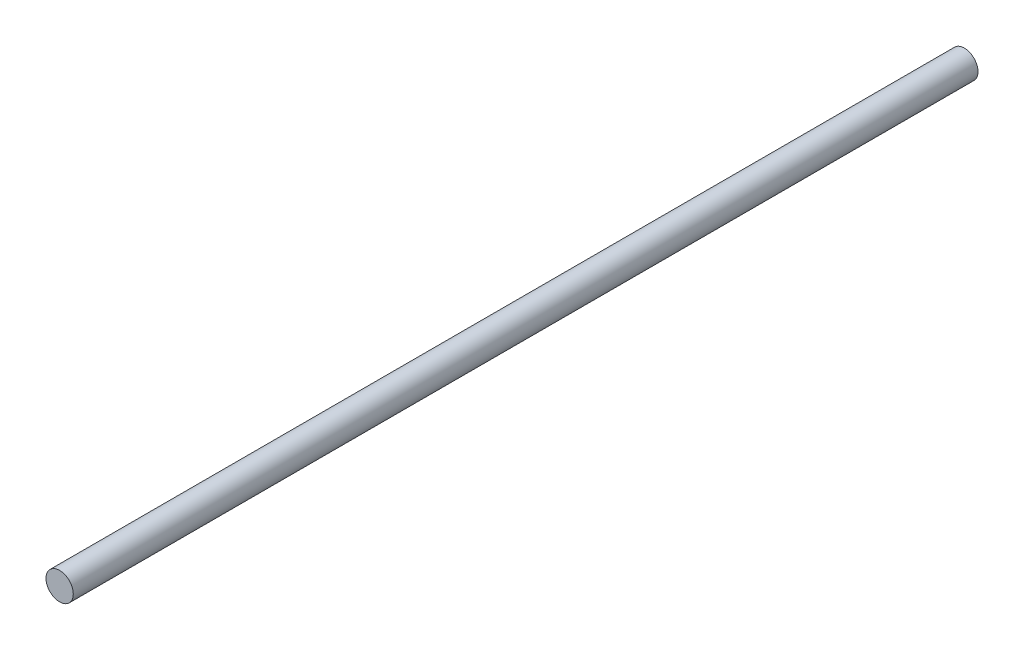
SolidWorks part; units mm, degrees
material "Alloy Steel"
ref_plane "Front Plane" through (0, 0, 0) normal (0, 0, 1) x (1, 0, 0)
ref_plane "Top Plane" through (0, 0, 0) normal (0, 1, 0) x (1, 0, 0)
ref_plane "Right Plane" through (0, 0, 0) normal (1, 0, 0) x (0, 0, -1)
sketch "Sketch1" plane through (0, 0, 0) normal (0, 0, 1) x (1, 0, 0)
  circle A0 centre (0, 0) radius 3.175
  dimension "D1" = 6.35
extrude "Boss-Extrude1" add sketch "Sketch1" along normal blind 210.3628
